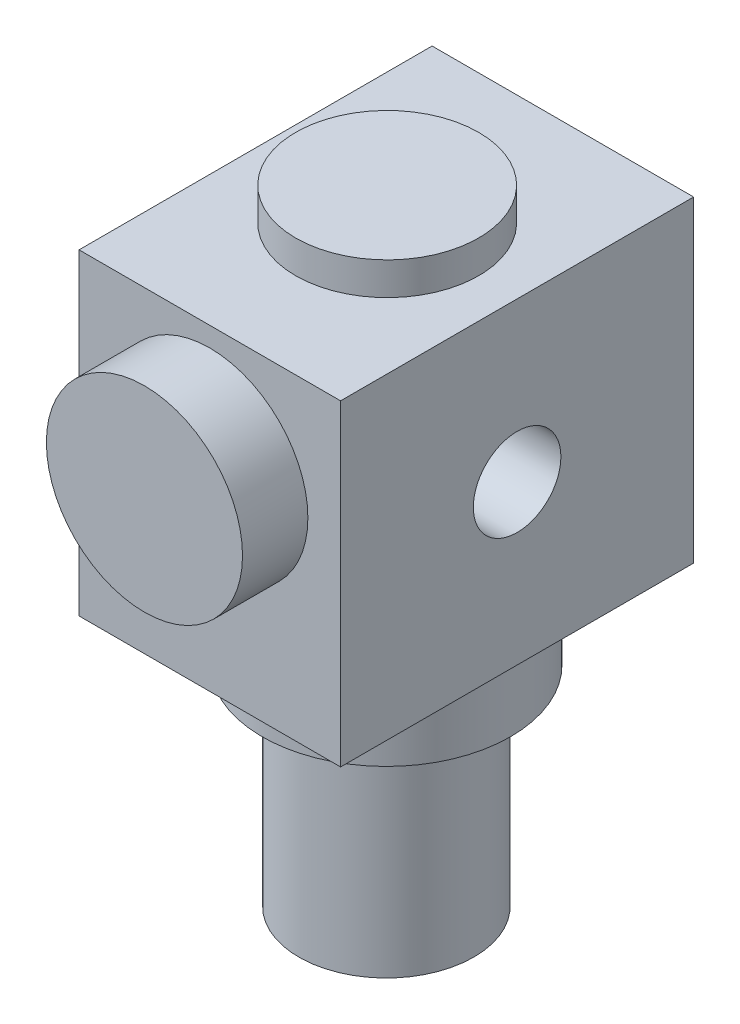
SolidWorks part; units mm, degrees
ref_plane "Front Plane" through (0, 0, 0) normal (1, 0, 0) x (0, 1, 0)
ref_plane "Top Plane" through (0, 0, 0) normal (0, 0, 1) x (0, 1, 0)
ref_plane "Right Plane" through (0, 0, 0) normal (0, 1, 0) x (-1, 0, 0)
sketch "Sketch1" plane through (0, 0, 0) normal (0, 0, 1) x (0, 1, 0)
  line L1 (-24.25, 20) -> (24.25, 20)
  line L2 (-24.25, 20) -> (-24.25, -20)
  line L3 (-24.25, -20) -> (24.25, -20)
  line L4 (24.25, 20) -> (24.25, -20)
  line L5 (-24.25, 20) -> (24.25, -20) construction
  line L6 (-24.25, -20) -> (24.25, 20) construction
  point P0 (0, 0)
  dimension "D1" = 48.5
  dimension "D2" = 40
extrude "Boss-Extrude1" add sketch "Sketch1" along normal blind 54
sketch "Sketch2" plane through (0, 0, 54) normal (0, 0, 1) x (1, 0, 0)
  line L0 (20, 24.25) -> (-20, 24.25) construction
  circle A0 centre (0, 6.25) radius 15
  point P4 (0, 0)
  dimension "D1" = 30
  dimension "D2" = 18
extrude "Boss-Extrude2" add sketch "Sketch2" along normal blind 10
sketch "Sketch3" plane through (0, 24.25, 0) normal (0, 1, 0) x (-1, 0, 0)
  line L0 (0, 54) -> (0, -0.2535) construction
  line L1 (-20, 54) -> (20, 54) construction
  circle A0 centre (0, 26.8733) radius 14
  point P7 (0, 0)
  point P8 (0, 26.8733)
  dimension "D1" = 28
extrude "Boss-Extrude3" add sketch "Sketch3" along normal blind 5
sketch "Sketch4" plane through (0, -24.25, 0) normal (0, -1, 0) x (1, 0, 0)
  line L0 (0, 54) -> (0, 0) construction
  line L1 (-20, 54) -> (20, 54) construction
  line L2 (-20, 0) -> (20, 0) construction
  circle A0 centre (0, 27) radius 19
  point P6 (0, 27)
  dimension "D1" = 38
extrude "Boss-Extrude4" add sketch "Sketch4" along normal blind 10
sketch "Sketch5" plane through (0, -34.25, 0) normal (0, -1, 0) x (1, 0, 0)
  circle A0 centre (0, 27) radius 13.3859
  dimension "D1" = 26.7718
extrude "Boss-Extrude5" add sketch "Sketch5" along normal blind 32
sketch "Sketch6" plane through (20, 0, 0) normal (1, 0, 0) x (0, 1, 0)
  line L0 (0, 54) -> (0, 0) construction
  line L1 (-24.25, 54) -> (24.25, 54) construction
  line L2 (-24.25, 0) -> (24.25, 0) construction
  circle A0 centre (0, 27) radius 6.7
  point P6 (0, 27)
  dimension "D1" = 13.4
extrude "Cut-Extrude1" cut sketch "Sketch6" against normal blind 20
sketch "Sketch7" plane through (-20, 0, 0) normal (-1, 0, 0) x (0, -1, 0)
  line L0 (0, 54) -> (0, 0) construction
  line L1 (-24.25, 54) -> (24.25, 54) construction
  line L2 (-24.25, 0) -> (24.25, 0) construction
  circle A0 centre (0, 27) radius 6.7
  point P6 (0, 27)
  dimension "D1" = 13.4
extrude "Cut-Extrude2" cut sketch "Sketch7" against normal blind 20
